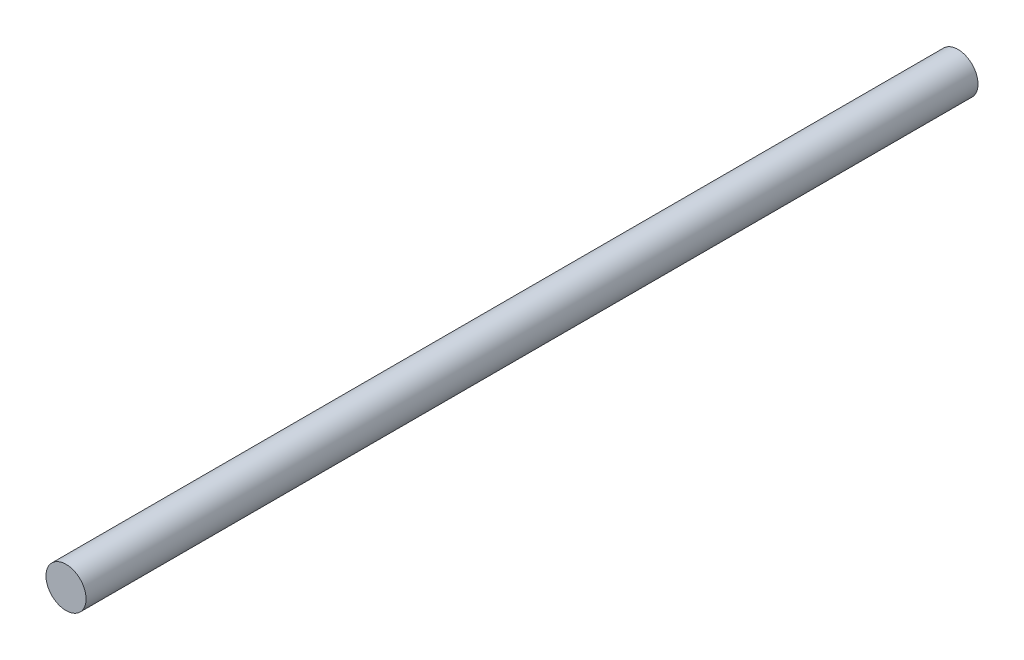
SolidWorks part; units mm, degrees
ref_plane "Front Plane" through (0, 0, 0) normal (0, 0, 1) x (1, 0, 0)
ref_plane "Top Plane" through (0, 0, 0) normal (0, 1, 0) x (1, 0, 0)
ref_plane "Right Plane" through (0, 0, 0) normal (1, 0, 0) x (0, 0, -1)
sketch "Sketch1" plane through (0, 0, 0) normal (0, 0, 1) x (1, 0, 0)
  circle A0 centre (0, 0) radius 4
  dimension "D1" = 8
extrude "Boss-Extrude1" add sketch "Sketch1" along normal mid plane 177.8
